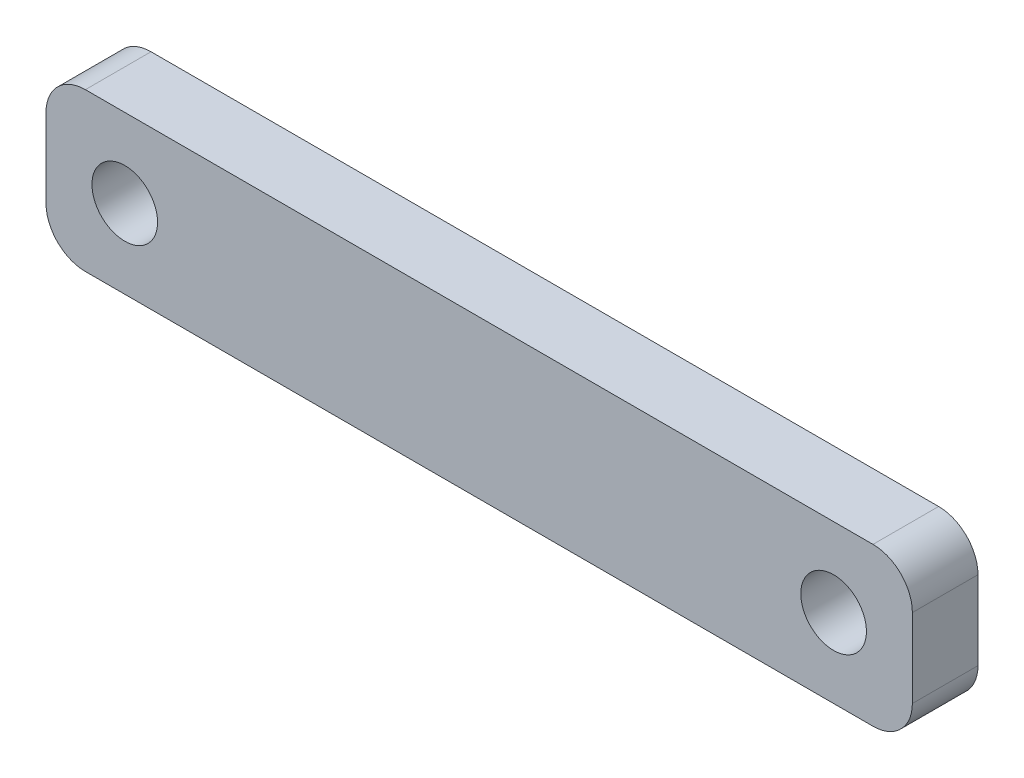
SolidWorks part; units mm, degrees
ref_plane "Спереди" through (0, 0, 0) normal (0, 0, 1) x (1, 0, 0)
ref_plane "Сверху" through (0, 0, 0) normal (0, 1, 0) x (1, 0, 0)
ref_plane "Справа" through (0, 0, 0) normal (1, 0, 0) x (0, 0, -1)
other "Configuration Table"
sketch "Sketch20" plane through (0, 0, 0) normal (0, 0, 1) x (1, 0, 0)
  line L0 (-22.0661, -5.0412) -> (37.9339, -5.0412)
  line L1 (40.9339, -8.0412) -> (40.9339, -14.0412)
  line L2 (37.9339, -17.0412) -> (-22.0661, -17.0412)
  line L3 (-25.0661, -14.0412) -> (-25.0661, -8.0412)
  line L4 (7.9339, 14.1911) -> (7.9339, -20.3289) construction
  arc A0 (37.9339, -5.0412) -> (40.9339, -8.0412) centre (37.9339, -8.0412) cw
  arc A1 (40.9339, -14.0412) -> (37.9339, -17.0412) centre (37.9339, -14.0412) cw
  arc A2 (-22.0661, -17.0412) -> (-25.0661, -14.0412) centre (-22.0661, -14.0412) cw
  arc A3 (-25.0661, -8.0412) -> (-22.0661, -5.0412) centre (-22.0661, -8.0412) cw
  circle A4 centre (-19.0661, -11.0412) radius 2.5
  circle A5 centre (34.9339, -11.0412) radius 2.5
  point P14 (-25.0661, -11.0412)
  point P19 (0, 0)
  point P20 (0, 0)
  dimension "D5" = 5
  dimension "D1" = 6
  dimension "D2" = 6
  dimension "D3" = 60
extrude "Boss-Extrude3" add sketch "Sketch20" along normal blind 5
